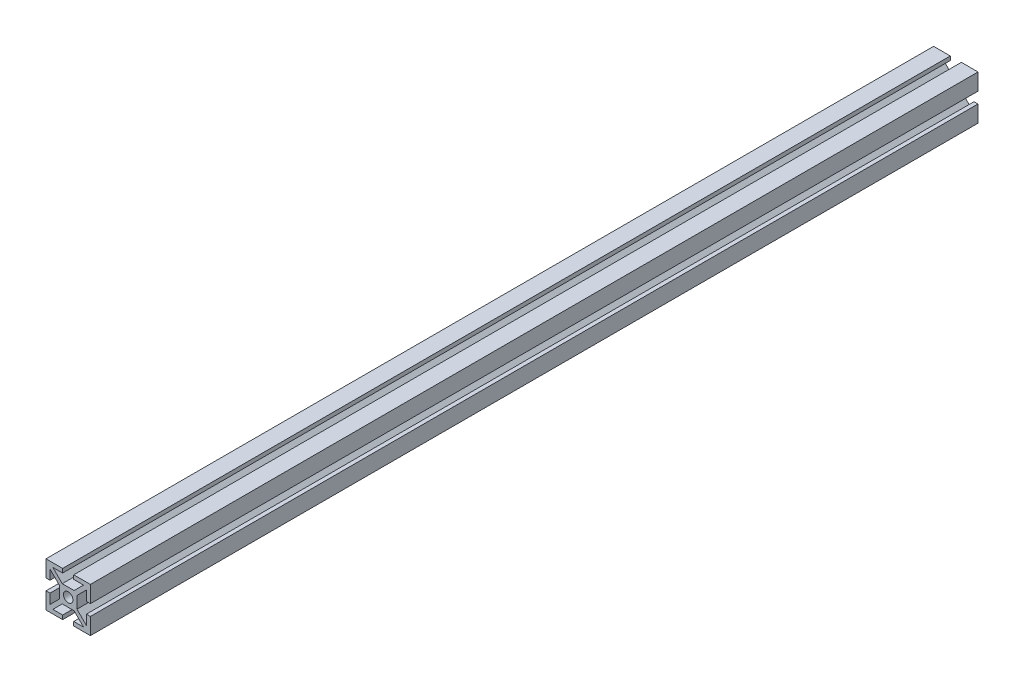
SolidWorks part; units mm, degrees
material "6063-T5"
ref_plane "Front Plane" through (0, 0, 0) normal (0, 0, 1) x (1, 0, 0)
ref_plane "Top Plane" through (0, 0, 0) normal (0, 1, 0) x (1, 0, 0)
ref_plane "Right Plane" through (0, 0, 0) normal (1, 0, 0) x (0, 0, -1)
sketch "Sketch2" plane through (0, 0, 0) normal (0, 0, 1) x (1, 0, 0)
  line L0 (-2.5, 10) -> (-2.5, 8.2)
  line L1 (-10, -10) -> (-2.5, -10)
  line L2 (-10, -10) -> (-10, -2.5)
  line L3 (-10, 10) -> (-2.5, 10)
  line L4 (10, -10) -> (10, -2.5)
  line L5 (-10, -10) -> (10, 10) construction
  line L6 (-10, 10) -> (10, -10) construction
  line L7 (-6.9272, -8.2) -> (-2.5, -8.2)
  line L8 (-8.2, -6.9272) -> (-8.2, -2.5)
  line L9 (-6.9272, 8.2) -> (-2.5, 8.2)
  line L10 (8.2, -6.9272) -> (8.2, -2.5)
  line L13 (2.5, 10) -> (2.5, 8.2)
  line L14 (2.5, 10) -> (10, 10)
  line L15 (2.5, 8.2) -> (6.9272, 8.2)
  line L16 (0, 0) -> (0, 17.5125) construction
  line L17 (-2.15, 2.15) -> (2.15, 2.15) construction
  line L18 (-2.6772, -3.95) -> (2.6772, -3.95)
  line L19 (-3.95, -2.6772) -> (-3.95, 2.6772)
  line L20 (-2.6772, 3.95) -> (2.6772, 3.95)
  line L21 (3.95, -2.6772) -> (3.95, 2.6772)
  line L24 (-2.6772, 3.95) -> (-6.9272, 8.2)
  line L25 (-3.95, 2.6772) -> (-8.2, 6.9272)
  line L26 (10, 2.5) -> (8.2, 2.5)
  line L27 (10, -2.5) -> (8.2, -2.5)
  line L28 (3.95, 2.6772) -> (8.2, 6.9272)
  line L29 (2.6772, 3.95) -> (6.9272, 8.2)
  line L30 (2.5, -10) -> (2.5, -8.2)
  line L31 (-2.5, -10) -> (-2.5, -8.2)
  line L32 (2.6772, -3.95) -> (6.9272, -8.2)
  line L33 (3.95, -2.6772) -> (8.2, -6.9272)
  line L34 (-10, -2.5) -> (-8.2, -2.5)
  line L35 (-10, 2.5) -> (-8.2, 2.5)
  line L36 (-3.95, -2.6772) -> (-8.2, -6.9272)
  line L37 (-2.6772, -3.95) -> (-6.9272, -8.2)
  line L38 (-10, 2.5) -> (-10, 10)
  line L39 (-8.2, 2.5) -> (-8.2, 6.9272)
  line L40 (10, 2.5) -> (10, 10)
  line L41 (8.2, 2.5) -> (8.2, 6.9272)
  line L42 (2.5, -8.2) -> (6.9272, -8.2)
  line L43 (2.5, -10) -> (10, -10)
  circle A0 centre (0, 0) radius 2.15
  point P0 (0, 0)
  point P54 (0, 0)
  dimension "D3" = 4.3
  dimension "D7" = 1.8
  dimension "D1" = 20
  dimension "D4" = 1.8
  dimension "D5" = 5
  dimension "D6" = 1.8
  dimension "D8" = 4
extrude "Boss-Extrude1" add sketch "Sketch2" along normal mid plane 400
